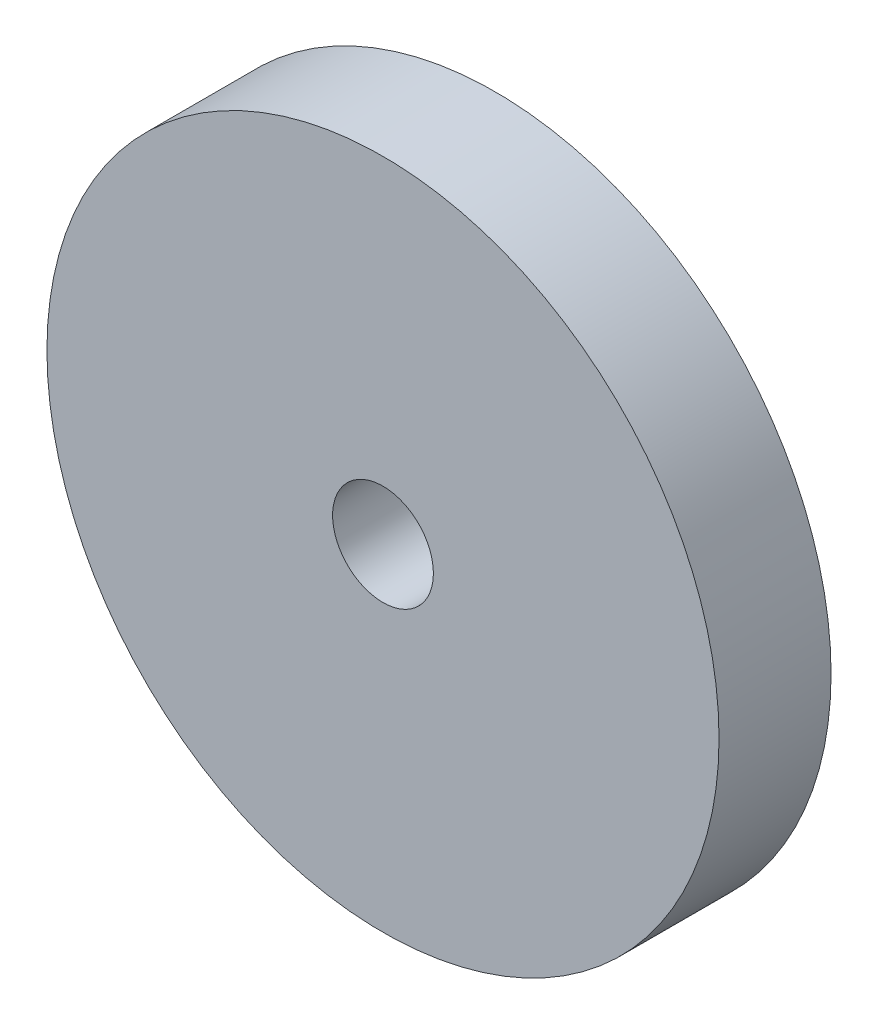
SolidWorks part; units mm, degrees
ref_plane "Front" through (0, 0, 0) normal (0, 0, 1) x (1, 0, 0)
ref_plane "Top" through (0, 0, 0) normal (0, 1, 0) x (1, 0, 0)
ref_plane "Right" through (0, 0, 0) normal (1, 0, 0) x (0, 0, -1)
sketch "Sketch1" plane through (0, 0, 0) normal (0, 0, 1) x (1, 0, 0)
  circle A0 centre (0, 0) radius 60
  circle A1 centre (0, 0) radius 9
  dimension "D1" = 18
  dimension "D2" = 120
extrude "Boss-Extrude1" add sketch "Sketch1" along normal blind 20
